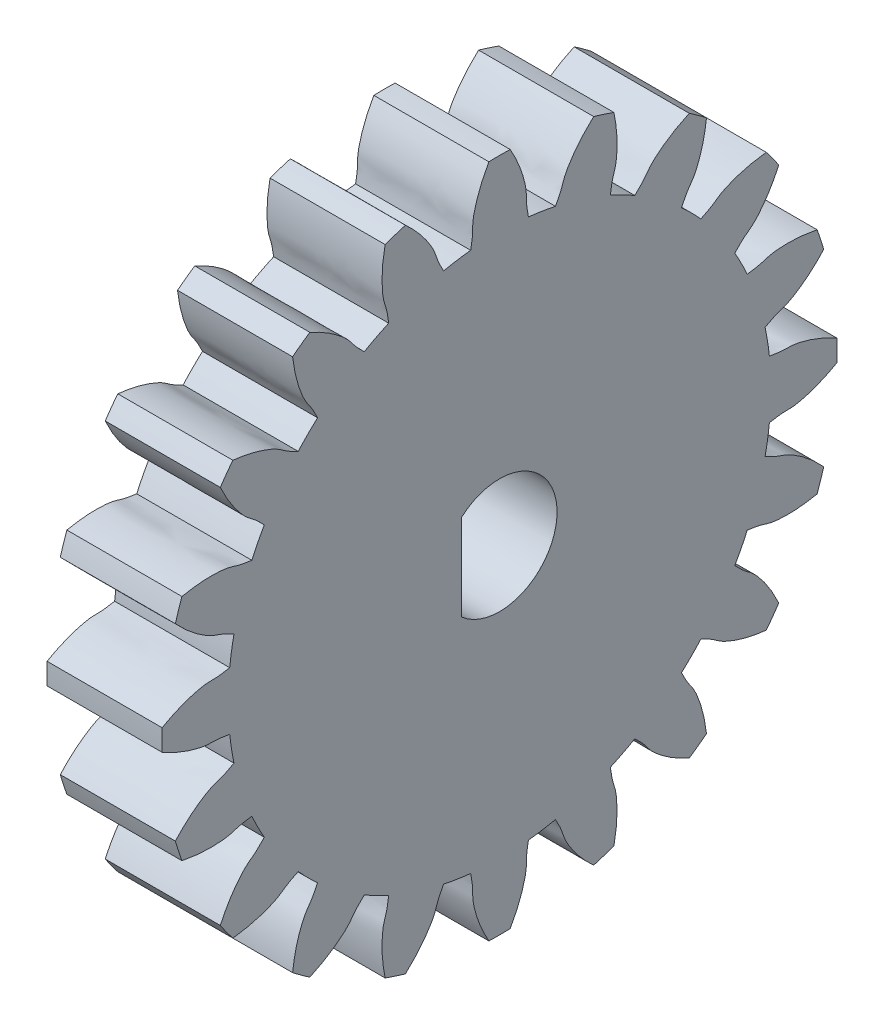
SolidWorks part; units mm, degrees
ref_plane "Front Plane" through (0, 0, 0) normal (0, 0, 1) x (1, 0, 0)
ref_plane "Top Plane" through (0, 0, 0) normal (0, 1, 0) x (1, 0, 0)
ref_plane "Right Plane" through (0, 0, 0) normal (1, 0, 0) x (0, 0, -1)
ref_plane "Plane1" through (0, 2.008, 0) normal (0, -1, 0) x (-1, 0, 0)
ref_plane "Plane2" through (0, 4.8333, 0) normal (0, 1, 0) x (1, 0, 0)
sketch "Sketch41" plane through (0, 0, 0) normal (0, 0, 1) x (1, 0, 0)
  line L0 (-1.5, 8.8) -> (-1.5, 0)
  line L1 (-1.5, 0) -> (1.5, 0)
  line L2 (1.5, 0) -> (1.5, 8.8)
  line L3 (1.5, 8.8) -> (-1.5, 8.8)
  line L4 (-1.5, 0) -> (1.5, 0) construction
revolve "Revolve3" add sketch "Sketch41" angle 360 about L1
ref_plane "Plane3" through (-1.5, 0, 0) normal (-1, 0, 0) x (0, 0, 1)
sketch "Sketch47" plane through (-1.5, 0, 0) normal (-1, 0, 0) x (0, 0, 1)
  arc A0 (0.7524, 7.0343) -> (1.4582, 6.9225) centre (0, 0) cw
  arc A1 (2.4537, 8.451) -> (0.2779, 8.7956) centre (0, 0) ccw
  spline S0 degree 3 poles (0.2779, 8.7956) (0.3159, 8.7284) (0.3523, 8.6603) (0.3868, 8.5913) (0.4678, 8.4292) (0.5382, 8.261) (0.5931, 8.0882) (0.6482, 7.9149) (0.6968, 7.7352) (0.7008, 7.5535) (0.7028, 7.4585) (0.7002, 7.3628) (0.7143, 7.2689) (0.7261, 7.1905) (0.7397, 7.1125) (0.7524, 7.0343) knots -0.000231 -0.000231 -0.000231 -0.000231 0 0 0 0.000544 0.000544 0.000544 0.001091 0.001091 0.001091 0.001372 0.001372 0.001372 0.001605 0.001605 0.001605 0.001605
  spline S1 degree 3 poles (1.4582, 6.9225) (1.4944, 6.9929) (1.5314, 7.063) (1.5669, 7.1338) (1.6364, 7.2729) (1.6675, 7.4295) (1.7404, 7.5668) (1.8106, 7.6992) (1.8949, 7.8242) (1.9854, 7.9436) (2.0779, 8.0657) (2.1795, 8.1812) (2.287, 8.2903) (2.3412, 8.3453) (2.3968, 8.3988) (2.4537, 8.451) knots -0.000237 -0.000237 -0.000237 -0.000237 0 0 0 0.000466 0.000466 0.000466 0.000915 0.000915 0.000915 0.001374 0.001374 0.001374 0.001605 0.001605 0.001605 0.001605
extrude "Cut-Extrude22" cut sketch "Sketch47" against normal through all
sketch "Sketch54" plane through (-1.5, 0, 0) normal (-1, 0, 0) x (0, 0, 1)
  arc A0 (2.8893, 6.4575) -> (3.526, 6.1331) centre (0, 0) cw
  arc A1 (4.9451, 7.2791) -> (2.9823, 8.2792) centre (0, 0) ccw
  spline S0 degree 3 poles (2.9823, 8.2792) (2.9976, 8.2036) (3.0112, 8.1276) (3.0227, 8.0513) (3.0497, 7.8721) (3.0646, 7.6903) (3.0635, 7.5091) (3.0623, 7.3272) (3.053, 7.1413) (3.0006, 6.9672) (2.9733, 6.8763) (2.9411, 6.7861) (2.9255, 6.6924) (2.9125, 6.6142) (2.9013, 6.5358) (2.8893, 6.4575) knots -0.000231 -0.000231 -0.000231 -0.000231 0 0 0 0.000544 0.000544 0.000544 0.001091 0.001091 0.001091 0.001372 0.001372 0.001372 0.001605 0.001605 0.001605 0.001605
  spline S1 degree 3 poles (3.526, 6.1331) (3.5822, 6.1889) (3.6391, 6.244) (3.6946, 6.3005) (3.8037, 6.4113) (3.8817, 6.5506) (3.9935, 6.6587) (4.1011, 6.7629) (4.22, 6.8557) (4.3429, 6.9413) (4.4686, 7.0288) (4.601, 7.1073) (4.7369, 7.1779) (4.8054, 7.2134) (4.8749, 7.2471) (4.9451, 7.2791) knots -0.000237 -0.000237 -0.000237 -0.000237 0 0 0 0.000466 0.000466 0.000466 0.000915 0.000915 0.000915 0.001374 0.001374 0.001374 0.001605 0.001605 0.001605 0.001605
extrude "Cut-Extrude23" cut sketch "Sketch54" against normal through all
sketch "Sketch61" plane through (-1.5, 0, 0) normal (-1, 0, 0) x (0, 0, 1)
  arc A0 (4.7433, 5.2486) -> (5.2486, 4.7433) centre (0, 0) cw
  arc A1 (6.9524, 5.3948) -> (5.3948, 6.9524) centre (0, 0) ccw
  spline S0 degree 3 poles (5.3948, 6.9524) (5.386, 6.8758) (5.3754, 6.7993) (5.3628, 6.7232) (5.3331, 6.5444) (5.2911, 6.3669) (5.234, 6.1949) (5.1767, 6.0223) (5.1104, 5.8484) (5.0068, 5.699) (4.9526, 5.6209) (4.8942, 5.5451) (4.8504, 5.4608) (4.8139, 5.3905) (4.779, 5.3194) (4.7433, 5.2486) knots -0.000231 -0.000231 -0.000231 -0.000231 0 0 0 0.000544 0.000544 0.000544 0.001091 0.001091 0.001091 0.001372 0.001372 0.001372 0.001605 0.001605 0.001605 0.001605
  spline S1 degree 3 poles (5.2486, 4.7433) (5.3194, 4.779) (5.3905, 4.8139) (5.4608, 4.8504) (5.5988, 4.9221) (5.716, 5.0305) (5.8557, 5.0987) (5.9903, 5.1645) (6.132, 5.2161) (6.2754, 5.2595) (6.422, 5.304) (6.572, 5.3376) (6.7232, 5.3628) (6.7993, 5.3754) (6.8758, 5.386) (6.9524, 5.3948) knots -0.000237 -0.000237 -0.000237 -0.000237 0 0 0 0.000466 0.000466 0.000466 0.000915 0.000915 0.000915 0.001374 0.001374 0.001374 0.001605 0.001605 0.001605 0.001605
extrude "Cut-Extrude24" cut sketch "Sketch61" against normal through all
sketch "Sketch68" plane through (-1.5, 0, 0) normal (-1, 0, 0) x (0, 0, 1)
  arc A0 (6.1331, 3.526) -> (6.4575, 2.8893) centre (0, 0) cw
  arc A1 (8.2792, 2.9823) -> (7.2791, 4.9451) centre (0, 0) ccw
  spline S0 degree 3 poles (7.2791, 4.9451) (7.2471, 4.8749) (7.2134, 4.8054) (7.1779, 4.7369) (7.0944, 4.5761) (6.9996, 4.4202) (6.8921, 4.2743) (6.7843, 4.1279) (6.6675, 3.9829) (6.5228, 3.8729) (6.4472, 3.8154) (6.3682, 3.7613) (6.3005, 3.6946) (6.244, 3.6391) (6.1889, 3.5822) (6.1331, 3.526) knots -0.000231 -0.000231 -0.000231 -0.000231 0 0 0 0.000544 0.000544 0.000544 0.001091 0.001091 0.001091 0.001372 0.001372 0.001372 0.001605 0.001605 0.001605 0.001605
  spline S1 degree 3 poles (6.4575, 2.8893) (6.5358, 2.9013) (6.6142, 2.9125) (6.6924, 2.9255) (6.8457, 2.9511) (6.9907, 3.0179) (7.1447, 3.0397) (7.293, 3.0607) (7.4437, 3.0659) (7.5935, 3.0629) (7.7466, 3.0599) (7.8998, 3.0455) (8.0513, 3.0227) (8.1276, 3.0112) (8.2036, 2.9976) (8.2792, 2.9823) knots -0.000237 -0.000237 -0.000237 -0.000237 0 0 0 0.000466 0.000466 0.000466 0.000915 0.000915 0.000915 0.001374 0.001374 0.001374 0.001605 0.001605 0.001605 0.001605
extrude "Cut-Extrude25" cut sketch "Sketch68" against normal through all
sketch "Sketch75" plane through (-1.5, 0, 0) normal (-1, 0, 0) x (0, 0, 1)
  arc A0 (6.9225, 1.4582) -> (7.0343, 0.7524) centre (0, 0) cw
  arc A1 (8.7956, 0.2779) -> (8.451, 2.4537) centre (0, 0) ccw
  spline S0 degree 3 poles (8.451, 2.4537) (8.3988, 2.3968) (8.3453, 2.3412) (8.2903, 2.287) (8.1612, 2.1598) (8.0229, 2.0409) (7.8756, 1.9353) (7.7279, 1.8294) (7.572, 1.7276) (7.4003, 1.6677) (7.3107, 1.6364) (7.2188, 1.6093) (7.1338, 1.5669) (7.063, 1.5314) (6.9929, 1.4944) (6.9225, 1.4582) knots -0.000231 -0.000231 -0.000231 -0.000231 0 0 0 0.000544 0.000544 0.000544 0.001091 0.001091 0.001091 0.001372 0.001372 0.001372 0.001605 0.001605 0.001605 0.001605
  spline S1 degree 3 poles (7.0343, 0.7524) (7.1125, 0.7397) (7.1905, 0.7261) (7.2689, 0.7143) (7.4226, 0.6912) (7.5811, 0.71) (7.7343, 0.6831) (7.8819, 0.6572) (8.0268, 0.6156) (8.1683, 0.5665) (8.3131, 0.5163) (8.4543, 0.4553) (8.5913, 0.3868) (8.6603, 0.3523) (8.7284, 0.3159) (8.7956, 0.2779) knots -0.000237 -0.000237 -0.000237 -0.000237 0 0 0 0.000466 0.000466 0.000466 0.000915 0.000915 0.000915 0.001374 0.001374 0.001374 0.001605 0.001605 0.001605 0.001605
extrude "Cut-Extrude26" cut sketch "Sketch75" against normal through all
sketch "Sketch82" plane through (-1.5, 0, 0) normal (-1, 0, 0) x (0, 0, 1)
  arc A0 (8.451, -2.4537) -> (8.7956, -0.2779) centre (0, 0) ccw
  arc A1 (7.0343, -0.7524) -> (6.9225, -1.4582) centre (0, 0) cw
  spline S0 degree 3 poles (8.7956, -0.2779) (8.7284, -0.3159) (8.6603, -0.3523) (8.5913, -0.3868) (8.4292, -0.4678) (8.261, -0.5382) (8.0882, -0.5931) (7.9149, -0.6482) (7.7352, -0.6968) (7.5535, -0.7008) (7.4585, -0.7028) (7.3628, -0.7002) (7.2689, -0.7143) (7.1905, -0.7261) (7.1125, -0.7397) (7.0343, -0.7524) knots -0.000231 -0.000231 -0.000231 -0.000231 0 0 0 0.000544 0.000544 0.000544 0.001091 0.001091 0.001091 0.001372 0.001372 0.001372 0.001605 0.001605 0.001605 0.001605
  spline S1 degree 3 poles (6.9225, -1.4582) (6.9929, -1.4944) (7.063, -1.5314) (7.1338, -1.5669) (7.2729, -1.6364) (7.4295, -1.6675) (7.5668, -1.7404) (7.6992, -1.8106) (7.8242, -1.8949) (7.9436, -1.9854) (8.0657, -2.0779) (8.1812, -2.1795) (8.2903, -2.287) (8.3453, -2.3412) (8.3988, -2.3968) (8.451, -2.4537) knots -0.000237 -0.000237 -0.000237 -0.000237 0 0 0 0.000466 0.000466 0.000466 0.000915 0.000915 0.000915 0.001374 0.001374 0.001374 0.001605 0.001605 0.001605 0.001605
extrude "Cut-Extrude27" cut sketch "Sketch82" against normal through all
sketch "Sketch89" plane through (-1.5, 0, 0) normal (-1, 0, 0) x (0, 0, 1)
  arc A0 (7.2791, -4.9451) -> (8.2792, -2.9823) centre (0, 0) ccw
  arc A1 (6.4575, -2.8893) -> (6.1331, -3.526) centre (0, 0) cw
  spline S0 degree 3 poles (8.2792, -2.9823) (8.2036, -2.9976) (8.1276, -3.0112) (8.0513, -3.0227) (7.8721, -3.0497) (7.6903, -3.0646) (7.5091, -3.0635) (7.3272, -3.0623) (7.1413, -3.053) (6.9672, -3.0006) (6.8763, -2.9733) (6.7861, -2.9411) (6.6924, -2.9255) (6.6142, -2.9125) (6.5358, -2.9013) (6.4575, -2.8893) knots -0.000231 -0.000231 -0.000231 -0.000231 0 0 0 0.000544 0.000544 0.000544 0.001091 0.001091 0.001091 0.001372 0.001372 0.001372 0.001605 0.001605 0.001605 0.001605
  spline S1 degree 3 poles (6.1331, -3.526) (6.1889, -3.5822) (6.244, -3.6391) (6.3005, -3.6946) (6.4113, -3.8037) (6.5506, -3.8817) (6.6587, -3.9935) (6.7629, -4.1011) (6.8557, -4.22) (6.9413, -4.3429) (7.0288, -4.4686) (7.1073, -4.601) (7.1779, -4.7369) (7.2134, -4.8054) (7.2471, -4.8749) (7.2791, -4.9451) knots -0.000237 -0.000237 -0.000237 -0.000237 0 0 0 0.000466 0.000466 0.000466 0.000915 0.000915 0.000915 0.001374 0.001374 0.001374 0.001605 0.001605 0.001605 0.001605
extrude "Cut-Extrude28" cut sketch "Sketch89" against normal through all
sketch "Sketch96" plane through (-1.5, 0, 0) normal (-1, 0, 0) x (0, 0, 1)
  arc A0 (5.3948, -6.9524) -> (6.9524, -5.3948) centre (0, 0) ccw
  arc A1 (5.2486, -4.7433) -> (4.7433, -5.2486) centre (0, 0) cw
  spline S0 degree 3 poles (6.9524, -5.3948) (6.8758, -5.386) (6.7993, -5.3754) (6.7232, -5.3628) (6.5444, -5.3331) (6.3669, -5.2911) (6.1949, -5.234) (6.0223, -5.1767) (5.8484, -5.1104) (5.699, -5.0068) (5.6209, -4.9526) (5.5451, -4.8942) (5.4608, -4.8504) (5.3905, -4.8139) (5.3194, -4.779) (5.2486, -4.7433) knots -0.000231 -0.000231 -0.000231 -0.000231 0 0 0 0.000544 0.000544 0.000544 0.001091 0.001091 0.001091 0.001372 0.001372 0.001372 0.001605 0.001605 0.001605 0.001605
  spline S1 degree 3 poles (4.7433, -5.2486) (4.779, -5.3194) (4.8139, -5.3905) (4.8504, -5.4608) (4.9221, -5.5988) (5.0305, -5.716) (5.0987, -5.8557) (5.1645, -5.9903) (5.2161, -6.132) (5.2595, -6.2754) (5.304, -6.422) (5.3376, -6.572) (5.3628, -6.7232) (5.3754, -6.7993) (5.386, -6.8758) (5.3948, -6.9524) knots -0.000237 -0.000237 -0.000237 -0.000237 0 0 0 0.000466 0.000466 0.000466 0.000915 0.000915 0.000915 0.001374 0.001374 0.001374 0.001605 0.001605 0.001605 0.001605
extrude "Cut-Extrude29" cut sketch "Sketch96" against normal through all
sketch "Sketch103" plane through (-1.5, 0, 0) normal (-1, 0, 0) x (0, 0, 1)
  arc A0 (2.9823, -8.2792) -> (4.9451, -7.2791) centre (0, 0) ccw
  arc A1 (3.526, -6.1331) -> (2.8893, -6.4575) centre (0, 0) cw
  spline S0 degree 3 poles (4.9451, -7.2791) (4.8749, -7.2471) (4.8054, -7.2134) (4.7369, -7.1779) (4.5761, -7.0944) (4.4202, -6.9996) (4.2743, -6.8921) (4.1279, -6.7843) (3.9829, -6.6675) (3.8729, -6.5228) (3.8154, -6.4472) (3.7613, -6.3682) (3.6946, -6.3005) (3.6391, -6.244) (3.5822, -6.1889) (3.526, -6.1331) knots -0.000231 -0.000231 -0.000231 -0.000231 0 0 0 0.000544 0.000544 0.000544 0.001091 0.001091 0.001091 0.001372 0.001372 0.001372 0.001605 0.001605 0.001605 0.001605
  spline S1 degree 3 poles (2.8893, -6.4575) (2.9013, -6.5358) (2.9125, -6.6142) (2.9255, -6.6924) (2.9511, -6.8457) (3.0179, -6.9907) (3.0397, -7.1447) (3.0607, -7.293) (3.0659, -7.4437) (3.0629, -7.5935) (3.0599, -7.7466) (3.0455, -7.8998) (3.0227, -8.0513) (3.0112, -8.1276) (2.9976, -8.2036) (2.9823, -8.2792) knots -0.000237 -0.000237 -0.000237 -0.000237 0 0 0 0.000466 0.000466 0.000466 0.000915 0.000915 0.000915 0.001374 0.001374 0.001374 0.001605 0.001605 0.001605 0.001605
extrude "Cut-Extrude30" cut sketch "Sketch103" against normal through all
sketch "Sketch110" plane through (-1.5, 0, 0) normal (-1, 0, 0) x (0, 0, 1)
  arc A0 (0.2779, -8.7956) -> (2.4537, -8.451) centre (0, 0) ccw
  arc A1 (1.4582, -6.9225) -> (0.7524, -7.0343) centre (0, 0) cw
  spline S0 degree 3 poles (2.4537, -8.451) (2.3968, -8.3988) (2.3412, -8.3453) (2.287, -8.2903) (2.1598, -8.1612) (2.0409, -8.0229) (1.9353, -7.8756) (1.8294, -7.7279) (1.7276, -7.572) (1.6677, -7.4003) (1.6364, -7.3107) (1.6093, -7.2188) (1.5669, -7.1338) (1.5314, -7.063) (1.4944, -6.9929) (1.4582, -6.9225) knots -0.000231 -0.000231 -0.000231 -0.000231 0 0 0 0.000544 0.000544 0.000544 0.001091 0.001091 0.001091 0.001372 0.001372 0.001372 0.001605 0.001605 0.001605 0.001605
  spline S1 degree 3 poles (0.7524, -7.0343) (0.7397, -7.1125) (0.7261, -7.1905) (0.7143, -7.2689) (0.6912, -7.4226) (0.71, -7.5811) (0.6831, -7.7343) (0.6572, -7.8819) (0.6156, -8.0268) (0.5665, -8.1683) (0.5163, -8.3131) (0.4553, -8.4543) (0.3868, -8.5913) (0.3523, -8.6603) (0.3159, -8.7284) (0.2779, -8.7956) knots -0.000237 -0.000237 -0.000237 -0.000237 0 0 0 0.000466 0.000466 0.000466 0.000915 0.000915 0.000915 0.001374 0.001374 0.001374 0.001605 0.001605 0.001605 0.001605
extrude "Cut-Extrude31" cut sketch "Sketch110" against normal through all
sketch "Sketch117" plane through (-1.5, 0, 0) normal (-1, 0, 0) x (0, 0, 1)
  arc A0 (-0.7524, -7.0343) -> (-1.4582, -6.9225) centre (0, 0) cw
  arc A1 (-2.4537, -8.451) -> (-0.2779, -8.7956) centre (0, 0) ccw
  spline S0 degree 3 poles (-0.2779, -8.7956) (-0.3159, -8.7284) (-0.3523, -8.6603) (-0.3868, -8.5913) (-0.4678, -8.4292) (-0.5382, -8.261) (-0.5931, -8.0882) (-0.6482, -7.9149) (-0.6968, -7.7352) (-0.7008, -7.5535) (-0.7028, -7.4585) (-0.7002, -7.3628) (-0.7143, -7.2689) (-0.7261, -7.1905) (-0.7397, -7.1125) (-0.7524, -7.0343) knots -0.000231 -0.000231 -0.000231 -0.000231 0 0 0 0.000544 0.000544 0.000544 0.001091 0.001091 0.001091 0.001372 0.001372 0.001372 0.001605 0.001605 0.001605 0.001605
  spline S1 degree 3 poles (-1.4582, -6.9225) (-1.4944, -6.9929) (-1.5314, -7.063) (-1.5669, -7.1338) (-1.6364, -7.2729) (-1.6675, -7.4295) (-1.7404, -7.5668) (-1.8106, -7.6992) (-1.8949, -7.8242) (-1.9854, -7.9436) (-2.0779, -8.0657) (-2.1795, -8.1812) (-2.287, -8.2903) (-2.3412, -8.3453) (-2.3968, -8.3988) (-2.4537, -8.451) knots -0.000237 -0.000237 -0.000237 -0.000237 0 0 0 0.000466 0.000466 0.000466 0.000915 0.000915 0.000915 0.001374 0.001374 0.001374 0.001605 0.001605 0.001605 0.001605
extrude "Cut-Extrude32" cut sketch "Sketch117" against normal through all
sketch "Sketch124" plane through (-1.5, 0, 0) normal (-1, 0, 0) x (0, 0, 1)
  arc A0 (-2.8893, -6.4575) -> (-3.526, -6.1331) centre (0, 0) cw
  arc A1 (-4.9451, -7.2791) -> (-2.9823, -8.2792) centre (0, 0) ccw
  spline S0 degree 3 poles (-2.9823, -8.2792) (-2.9976, -8.2036) (-3.0112, -8.1276) (-3.0227, -8.0513) (-3.0497, -7.8721) (-3.0646, -7.6903) (-3.0635, -7.5091) (-3.0623, -7.3272) (-3.053, -7.1413) (-3.0006, -6.9672) (-2.9733, -6.8763) (-2.9411, -6.7861) (-2.9255, -6.6924) (-2.9125, -6.6142) (-2.9013, -6.5358) (-2.8893, -6.4575) knots -0.000231 -0.000231 -0.000231 -0.000231 0 0 0 0.000544 0.000544 0.000544 0.001091 0.001091 0.001091 0.001372 0.001372 0.001372 0.001605 0.001605 0.001605 0.001605
  spline S1 degree 3 poles (-3.526, -6.1331) (-3.5822, -6.1889) (-3.6391, -6.244) (-3.6946, -6.3005) (-3.8037, -6.4113) (-3.8817, -6.5506) (-3.9935, -6.6587) (-4.1011, -6.7629) (-4.22, -6.8557) (-4.3429, -6.9413) (-4.4686, -7.0288) (-4.601, -7.1073) (-4.7369, -7.1779) (-4.8054, -7.2134) (-4.8749, -7.2471) (-4.9451, -7.2791) knots -0.000237 -0.000237 -0.000237 -0.000237 0 0 0 0.000466 0.000466 0.000466 0.000915 0.000915 0.000915 0.001374 0.001374 0.001374 0.001605 0.001605 0.001605 0.001605
extrude "Cut-Extrude33" cut sketch "Sketch124" against normal through all
sketch "Sketch131" plane through (-1.5, 0, 0) normal (-1, 0, 0) x (0, 0, 1)
  arc A0 (-6.9524, -5.3948) -> (-5.3948, -6.9524) centre (0, 0) ccw
  arc A1 (-4.7433, -5.2486) -> (-5.2486, -4.7433) centre (0, 0) cw
  spline S0 degree 3 poles (-5.3948, -6.9524) (-5.386, -6.8758) (-5.3754, -6.7993) (-5.3628, -6.7232) (-5.3331, -6.5444) (-5.2911, -6.3669) (-5.234, -6.1949) (-5.1767, -6.0223) (-5.1104, -5.8484) (-5.0068, -5.699) (-4.9526, -5.6209) (-4.8942, -5.5451) (-4.8504, -5.4608) (-4.8139, -5.3905) (-4.779, -5.3194) (-4.7433, -5.2486) knots -0.000231 -0.000231 -0.000231 -0.000231 0 0 0 0.000544 0.000544 0.000544 0.001091 0.001091 0.001091 0.001372 0.001372 0.001372 0.001605 0.001605 0.001605 0.001605
  spline S1 degree 3 poles (-5.2486, -4.7433) (-5.3194, -4.779) (-5.3905, -4.8139) (-5.4608, -4.8504) (-5.5988, -4.9221) (-5.716, -5.0305) (-5.8557, -5.0987) (-5.9903, -5.1645) (-6.132, -5.2161) (-6.2754, -5.2595) (-6.422, -5.304) (-6.572, -5.3376) (-6.7232, -5.3628) (-6.7993, -5.3754) (-6.8758, -5.386) (-6.9524, -5.3948) knots -0.000237 -0.000237 -0.000237 -0.000237 0 0 0 0.000466 0.000466 0.000466 0.000915 0.000915 0.000915 0.001374 0.001374 0.001374 0.001605 0.001605 0.001605 0.001605
extrude "Cut-Extrude34" cut sketch "Sketch131" against normal through all
sketch "Sketch138" plane through (-1.5, 0, 0) normal (-1, 0, 0) x (0, 0, 1)
  arc A0 (-8.2792, -2.9823) -> (-7.2791, -4.9451) centre (0, 0) ccw
  arc A1 (-6.1331, -3.526) -> (-6.4575, -2.8893) centre (0, 0) cw
  spline S0 degree 3 poles (-7.2791, -4.9451) (-7.2471, -4.8749) (-7.2134, -4.8054) (-7.1779, -4.7369) (-7.0944, -4.5761) (-6.9996, -4.4202) (-6.8921, -4.2743) (-6.7843, -4.1279) (-6.6675, -3.9829) (-6.5228, -3.8729) (-6.4472, -3.8154) (-6.3682, -3.7613) (-6.3005, -3.6946) (-6.244, -3.6391) (-6.1889, -3.5822) (-6.1331, -3.526) knots -0.000231 -0.000231 -0.000231 -0.000231 0 0 0 0.000544 0.000544 0.000544 0.001091 0.001091 0.001091 0.001372 0.001372 0.001372 0.001605 0.001605 0.001605 0.001605
  spline S1 degree 3 poles (-6.4575, -2.8893) (-6.5358, -2.9013) (-6.6142, -2.9125) (-6.6924, -2.9255) (-6.8457, -2.9511) (-6.9907, -3.0179) (-7.1447, -3.0397) (-7.293, -3.0607) (-7.4437, -3.0659) (-7.5935, -3.0629) (-7.7466, -3.0599) (-7.8998, -3.0455) (-8.0513, -3.0227) (-8.1276, -3.0112) (-8.2036, -2.9976) (-8.2792, -2.9823) knots -0.000237 -0.000237 -0.000237 -0.000237 0 0 0 0.000466 0.000466 0.000466 0.000915 0.000915 0.000915 0.001374 0.001374 0.001374 0.001605 0.001605 0.001605 0.001605
extrude "Cut-Extrude35" cut sketch "Sketch138" against normal through all
sketch "Sketch145" plane through (-1.5, 0, 0) normal (-1, 0, 0) x (0, 0, 1)
  arc A0 (-8.7956, -0.2779) -> (-8.451, -2.4537) centre (0, 0) ccw
  arc A1 (-6.9225, -1.4582) -> (-7.0343, -0.7524) centre (0, 0) cw
  spline S0 degree 3 poles (-8.451, -2.4537) (-8.3988, -2.3968) (-8.3453, -2.3412) (-8.2903, -2.287) (-8.1612, -2.1598) (-8.0229, -2.0409) (-7.8756, -1.9353) (-7.7279, -1.8294) (-7.572, -1.7276) (-7.4003, -1.6677) (-7.3107, -1.6364) (-7.2188, -1.6093) (-7.1338, -1.5669) (-7.063, -1.5314) (-6.9929, -1.4944) (-6.9225, -1.4582) knots -0.000231 -0.000231 -0.000231 -0.000231 0 0 0 0.000544 0.000544 0.000544 0.001091 0.001091 0.001091 0.001372 0.001372 0.001372 0.001605 0.001605 0.001605 0.001605
  spline S1 degree 3 poles (-7.0343, -0.7524) (-7.1125, -0.7397) (-7.1905, -0.7261) (-7.2689, -0.7143) (-7.4226, -0.6912) (-7.5811, -0.71) (-7.7343, -0.6831) (-7.8819, -0.6572) (-8.0268, -0.6156) (-8.1683, -0.5665) (-8.3131, -0.5163) (-8.4543, -0.4553) (-8.5913, -0.3868) (-8.6603, -0.3523) (-8.7284, -0.3159) (-8.7956, -0.2779) knots -0.000237 -0.000237 -0.000237 -0.000237 0 0 0 0.000466 0.000466 0.000466 0.000915 0.000915 0.000915 0.001374 0.001374 0.001374 0.001605 0.001605 0.001605 0.001605
extrude "Cut-Extrude36" cut sketch "Sketch145" against normal through all
sketch "Sketch152" plane through (-1.5, 0, 0) normal (-1, 0, 0) x (0, 0, 1)
  arc A0 (-8.451, 2.4537) -> (-8.7956, 0.2779) centre (0, 0) ccw
  arc A1 (-7.0343, 0.7524) -> (-6.9225, 1.4582) centre (0, 0) cw
  spline S0 degree 3 poles (-8.7956, 0.2779) (-8.7284, 0.3159) (-8.6603, 0.3523) (-8.5913, 0.3868) (-8.4292, 0.4678) (-8.261, 0.5382) (-8.0882, 0.5931) (-7.9149, 0.6482) (-7.7352, 0.6968) (-7.5535, 0.7008) (-7.4585, 0.7028) (-7.3628, 0.7002) (-7.2689, 0.7143) (-7.1905, 0.7261) (-7.1125, 0.7397) (-7.0343, 0.7524) knots -0.000231 -0.000231 -0.000231 -0.000231 0 0 0 0.000544 0.000544 0.000544 0.001091 0.001091 0.001091 0.001372 0.001372 0.001372 0.001605 0.001605 0.001605 0.001605
  spline S1 degree 3 poles (-6.9225, 1.4582) (-6.9929, 1.4944) (-7.063, 1.5314) (-7.1338, 1.5669) (-7.2729, 1.6364) (-7.4295, 1.6675) (-7.5668, 1.7404) (-7.6992, 1.8106) (-7.8242, 1.8949) (-7.9436, 1.9854) (-8.0657, 2.0779) (-8.1812, 2.1795) (-8.2903, 2.287) (-8.3453, 2.3412) (-8.3988, 2.3968) (-8.451, 2.4537) knots -0.000237 -0.000237 -0.000237 -0.000237 0 0 0 0.000466 0.000466 0.000466 0.000915 0.000915 0.000915 0.001374 0.001374 0.001374 0.001605 0.001605 0.001605 0.001605
extrude "Cut-Extrude37" cut sketch "Sketch152" against normal through all
sketch "Sketch159" plane through (-1.5, 0, 0) normal (-1, 0, 0) x (0, 0, 1)
  arc A0 (-7.2791, 4.9451) -> (-8.2792, 2.9823) centre (0, 0) ccw
  arc A1 (-6.4575, 2.8893) -> (-6.1331, 3.526) centre (0, 0) cw
  spline S0 degree 3 poles (-8.2792, 2.9823) (-8.2036, 2.9976) (-8.1276, 3.0112) (-8.0513, 3.0227) (-7.8721, 3.0497) (-7.6903, 3.0646) (-7.5091, 3.0635) (-7.3272, 3.0623) (-7.1413, 3.053) (-6.9672, 3.0006) (-6.8763, 2.9733) (-6.7861, 2.9411) (-6.6924, 2.9255) (-6.6142, 2.9125) (-6.5358, 2.9013) (-6.4575, 2.8893) knots -0.000231 -0.000231 -0.000231 -0.000231 0 0 0 0.000544 0.000544 0.000544 0.001091 0.001091 0.001091 0.001372 0.001372 0.001372 0.001605 0.001605 0.001605 0.001605
  spline S1 degree 3 poles (-6.1331, 3.526) (-6.1889, 3.5822) (-6.244, 3.6391) (-6.3005, 3.6946) (-6.4113, 3.8037) (-6.5506, 3.8817) (-6.6587, 3.9935) (-6.7629, 4.1011) (-6.8557, 4.22) (-6.9413, 4.3429) (-7.0288, 4.4686) (-7.1073, 4.601) (-7.1779, 4.7369) (-7.2134, 4.8054) (-7.2471, 4.8749) (-7.2791, 4.9451) knots -0.000237 -0.000237 -0.000237 -0.000237 0 0 0 0.000466 0.000466 0.000466 0.000915 0.000915 0.000915 0.001374 0.001374 0.001374 0.001605 0.001605 0.001605 0.001605
extrude "Cut-Extrude38" cut sketch "Sketch159" against normal through all
sketch "Sketch166" plane through (-1.5, 0, 0) normal (-1, 0, 0) x (0, 0, 1)
  arc A0 (-5.3948, 6.9524) -> (-6.9524, 5.3948) centre (0, 0) ccw
  arc A1 (-5.2486, 4.7433) -> (-4.7433, 5.2486) centre (0, 0) cw
  spline S0 degree 3 poles (-6.9524, 5.3948) (-6.8758, 5.386) (-6.7993, 5.3754) (-6.7232, 5.3628) (-6.5444, 5.3331) (-6.3669, 5.2911) (-6.1949, 5.234) (-6.0223, 5.1767) (-5.8484, 5.1104) (-5.699, 5.0068) (-5.6209, 4.9526) (-5.5451, 4.8942) (-5.4608, 4.8504) (-5.3905, 4.8139) (-5.3194, 4.779) (-5.2486, 4.7433) knots -0.000231 -0.000231 -0.000231 -0.000231 0 0 0 0.000544 0.000544 0.000544 0.001091 0.001091 0.001091 0.001372 0.001372 0.001372 0.001605 0.001605 0.001605 0.001605
  spline S1 degree 3 poles (-4.7433, 5.2486) (-4.779, 5.3194) (-4.8139, 5.3905) (-4.8504, 5.4608) (-4.9221, 5.5988) (-5.0305, 5.716) (-5.0987, 5.8557) (-5.1645, 5.9903) (-5.2161, 6.132) (-5.2595, 6.2754) (-5.304, 6.422) (-5.3376, 6.572) (-5.3628, 6.7232) (-5.3754, 6.7993) (-5.386, 6.8758) (-5.3948, 6.9524) knots -0.000237 -0.000237 -0.000237 -0.000237 0 0 0 0.000466 0.000466 0.000466 0.000915 0.000915 0.000915 0.001374 0.001374 0.001374 0.001605 0.001605 0.001605 0.001605
extrude "Cut-Extrude39" cut sketch "Sketch166" against normal through all
sketch "Sketch173" plane through (-1.5, 0, 0) normal (-1, 0, 0) x (0, 0, 1)
  arc A0 (-2.9823, 8.2792) -> (-4.9451, 7.2791) centre (0, 0) ccw
  arc A1 (-3.526, 6.1331) -> (-2.8893, 6.4575) centre (0, 0) cw
  spline S0 degree 3 poles (-4.9451, 7.2791) (-4.8749, 7.2471) (-4.8054, 7.2134) (-4.7369, 7.1779) (-4.5761, 7.0944) (-4.4202, 6.9996) (-4.2743, 6.8921) (-4.1279, 6.7843) (-3.9829, 6.6675) (-3.8729, 6.5228) (-3.8154, 6.4472) (-3.7613, 6.3682) (-3.6946, 6.3005) (-3.6391, 6.244) (-3.5822, 6.1889) (-3.526, 6.1331) knots -0.000231 -0.000231 -0.000231 -0.000231 0 0 0 0.000544 0.000544 0.000544 0.001091 0.001091 0.001091 0.001372 0.001372 0.001372 0.001605 0.001605 0.001605 0.001605
  spline S1 degree 3 poles (-2.8893, 6.4575) (-2.9013, 6.5358) (-2.9125, 6.6142) (-2.9255, 6.6924) (-2.9511, 6.8457) (-3.0179, 6.9907) (-3.0397, 7.1447) (-3.0607, 7.293) (-3.0659, 7.4437) (-3.0629, 7.5935) (-3.0599, 7.7466) (-3.0455, 7.8998) (-3.0227, 8.0513) (-3.0112, 8.1276) (-2.9976, 8.2036) (-2.9823, 8.2792) knots -0.000237 -0.000237 -0.000237 -0.000237 0 0 0 0.000466 0.000466 0.000466 0.000915 0.000915 0.000915 0.001374 0.001374 0.001374 0.001605 0.001605 0.001605 0.001605
extrude "Cut-Extrude40" cut sketch "Sketch173" against normal through all
sketch "Sketch180" plane through (-1.5, 0, 0) normal (-1, 0, 0) x (0, 0, 1)
  arc A0 (-0.2779, 8.7956) -> (-2.4537, 8.451) centre (0, 0) ccw
  arc A1 (-1.4582, 6.9225) -> (-0.7524, 7.0343) centre (0, 0) cw
  spline S0 degree 3 poles (-2.4537, 8.451) (-2.3968, 8.3988) (-2.3412, 8.3453) (-2.287, 8.2903) (-2.1598, 8.1612) (-2.0409, 8.0229) (-1.9353, 7.8756) (-1.8294, 7.7279) (-1.7276, 7.572) (-1.6677, 7.4003) (-1.6364, 7.3107) (-1.6093, 7.2188) (-1.5669, 7.1338) (-1.5314, 7.063) (-1.4944, 6.9929) (-1.4582, 6.9225) knots -0.000231 -0.000231 -0.000231 -0.000231 0 0 0 0.000544 0.000544 0.000544 0.001091 0.001091 0.001091 0.001372 0.001372 0.001372 0.001605 0.001605 0.001605 0.001605
  spline S1 degree 3 poles (-0.7524, 7.0343) (-0.7397, 7.1125) (-0.7261, 7.1905) (-0.7143, 7.2689) (-0.6912, 7.4226) (-0.71, 7.5811) (-0.6831, 7.7343) (-0.6572, 7.8819) (-0.6156, 8.0268) (-0.5665, 8.1683) (-0.5163, 8.3131) (-0.4553, 8.4543) (-0.3868, 8.5913) (-0.3523, 8.6603) (-0.3159, 8.7284) (-0.2779, 8.7956) knots -0.000237 -0.000237 -0.000237 -0.000237 0 0 0 0.000466 0.000466 0.000466 0.000915 0.000915 0.000915 0.001374 0.001374 0.001374 0.001605 0.001605 0.001605 0.001605
extrude "Cut-Extrude41" cut sketch "Sketch180" against normal through all
ref_plane "Plane4" through (1.5, 0, 0) normal (1, 0, 0) x (0, 0, -1)
sketch "Sketch192" plane through (-1.5, 0, 0) normal (-1, 0, 0) x (0, 0, 1)
  circle A0 centre (0, 0) radius 1.5
  dimension "D1" = 3
extrude "Cut-Extrude42" cut sketch "Sketch192" against normal through all
sketch "Sketch193" plane through (-1.5, 0, 0) normal (-1, 0, 0) x (0, 0, 1)
  line L0 (0.998, 1.1198) -> (0.998, -1.1198)
  circle A0 centre (0, 0) radius 1.5 construction
  arc A1 (0.998, -1.1198) -> (0.998, 1.1198) centre (0, 0) ccw
  dimension "D1" = 0.998
extrude "Boss-Extrude1" add sketch "Sketch193" against normal up to surface (3 mm away) up to face at (1.5, 0, 1.5)
